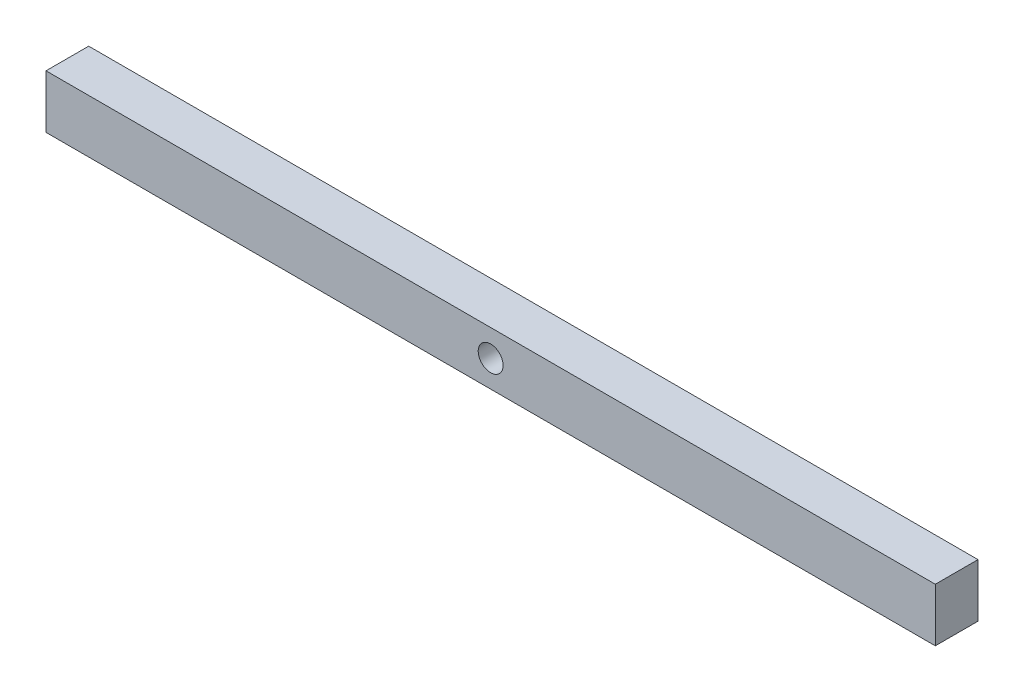
SolidWorks part; units mm, degrees
ref_plane "Front Plane" through (0, 0, 0) normal (0, 0, 1) x (1, 0, 0)
ref_plane "Top Plane" through (0, 0, 0) normal (0, 1, 0) x (1, 0, 0)
ref_plane "Right Plane" through (0, 0, 0) normal (1, 0, 0) x (0, 0, -1)
sketch "Sketch1" plane through (0, 0, 0) normal (0, 0, 1) x (1, 0, 0)
  line L0 (0, 3.81) -> (127, 3.81) construction
  line L1 (0, 0) -> (127, 0)
  line L2 (0, 0) -> (0, 7.62)
  line L3 (0, 7.62) -> (127, 7.62)
  line L4 (127, 0) -> (127, 7.62)
  line L5 (127, 3.81) -> (63.5, 7.62) construction
  line L6 (63.5, 7.62) -> (63.5, 0) construction
  line L7 (63.5, 0) -> (0, 3.81) construction
  circle A0 centre (63.5, 3.81) radius 1.778
  dimension "D3" = 3.556
  dimension "D1" = 127
  dimension "D2" = 7.62
extrude "Boss-Extrude1" add sketch "Sketch1" along normal blind 6.096
equation "\"mat\" = \"mat@fsc.assembly\""
equation "\"D1@Boss-Extrude1\"= \"mat\""
